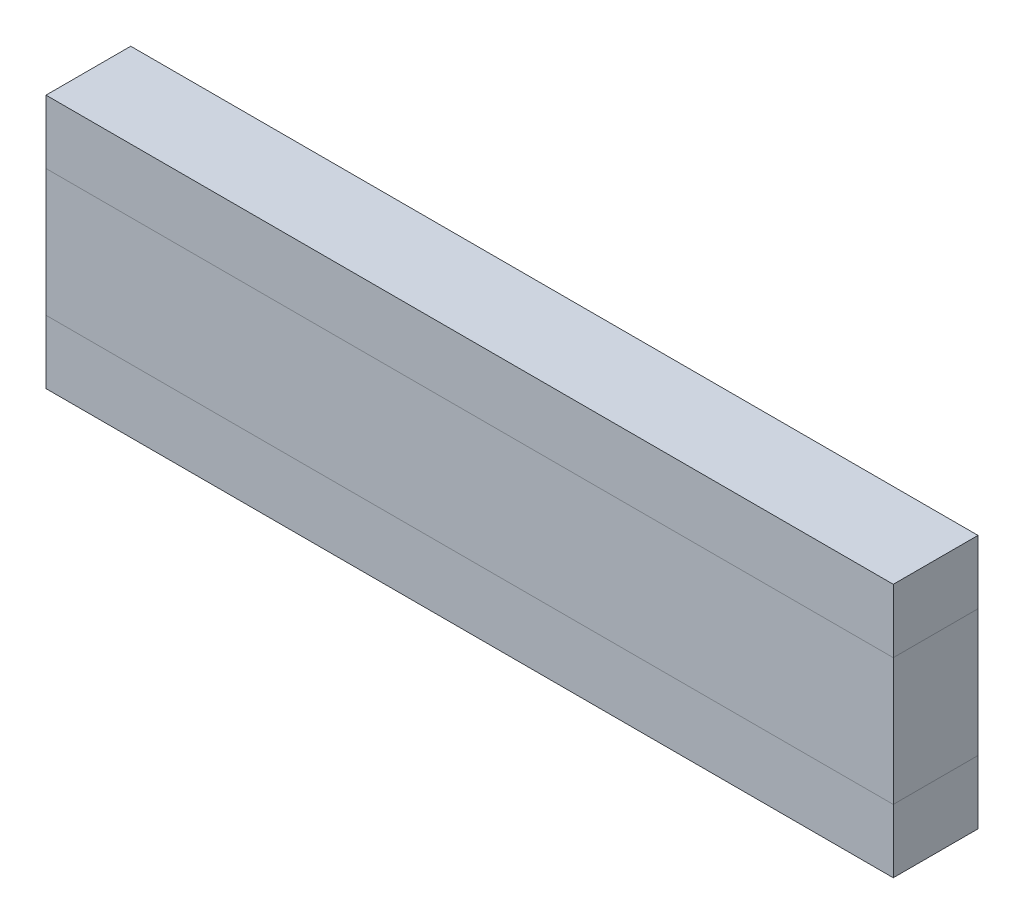
SolidWorks part; units mm, degrees
ref_plane "Vorne" through (0, 0, 0) normal (0, 0, 1) x (1, 0, 0)
ref_plane "Oben" through (0, 0, 0) normal (0, 1, 0) x (1, 0, 0)
ref_plane "Rechts" through (0, 0, 0) normal (1, 0, 0) x (0, 0, -1)
sketch "Skizze1" plane through (0, 0, 0) normal (0, 0, 1) x (1, 0, 0)
  line L1 (-50, 7.5) -> (50, 7.5)
  line L2 (-50, 7.5) -> (-50, -7.5)
  line L3 (-50, -7.5) -> (50, -7.5)
  line L4 (50, 7.5) -> (50, -7.5)
  line L5 (-50, 7.5) -> (50, -7.5) construction
  line L6 (-50, -7.5) -> (50, 7.5) construction
  point P0 (0, 0)
  dimension "D1" = 15
  dimension "D2" = 100
extrude "Aufsatz-Linear austragen1" add sketch "Skizze1" along normal mid plane 10
sketch "Skizze2" plane through (0, 0, 0) normal (0, 0, 1) x (1, 0, 0)
  line L0 (-50, 7.5) -> (-50, -7.5) construction
  line L1 (-50, 7.5) -> (50, 7.5)
  line L2 (-50, 7.5) -> (-50, 15)
  line L3 (-50, 15) -> (50, 15)
  line L4 (50, 7.5) -> (50, 15)
  line L5 (-50, -7.5) -> (50, -7.5)
  line L6 (-50, -7.5) -> (-50, -15)
  line L7 (-50, -15) -> (50, -15)
  line L8 (50, -7.5) -> (50, -15)
  line L9 (50, -7.5) -> (50, 7.5) construction
  line L10 (50, 7.5) -> (-50, 7.5) construction
  line L11 (-50, -7.5) -> (50, -7.5) construction
  dimension "D1" = 30
  dimension "D2" = 7.5
extrude "Aufsatz-Linear austragen2" add sketch "Skizze2" along normal up to surface and the other way up to surface separate body up to face at (0, 0, 5) other way up to face at (0, 0, -5)
